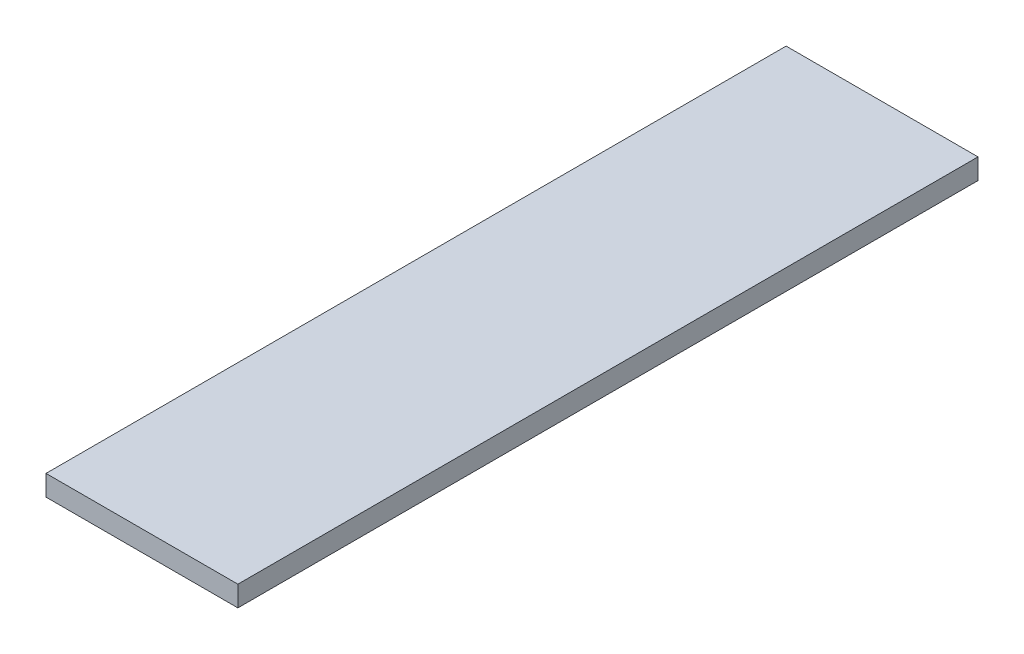
SolidWorks part; units mm, degrees
material "Pine"
ref_plane "Front Plane" through (0, 0, 0) normal (0, 0, 1) x (1, 0, 0)
ref_plane "Top Plane" through (0, 0, 0) normal (0, 1, 0) x (1, 0, 0)
ref_plane "Right Plane" through (0, 0, 0) normal (1, 0, 0) x (0, 0, -1)
sketch "Sketch1" plane through (0, 0, 0) normal (0, 1, 0) x (1, 0, 0)
  line L1 (-88.9, 342.9) -> (88.9, 342.9)
  line L2 (-88.9, 342.9) -> (-88.9, -342.9)
  line L3 (-88.9, -342.9) -> (88.9, -342.9)
  line L4 (88.9, 342.9) -> (88.9, -342.9)
  line L5 (-88.9, 342.9) -> (88.9, -342.9) construction
  line L6 (-88.9, -342.9) -> (88.9, 342.9) construction
  point P0 (0, 0)
  dimension "D1" = 685.8
  dimension "D2" = 177.8
extrude "Boss-Extrude1" add sketch "Sketch1" along normal blind 19.05
